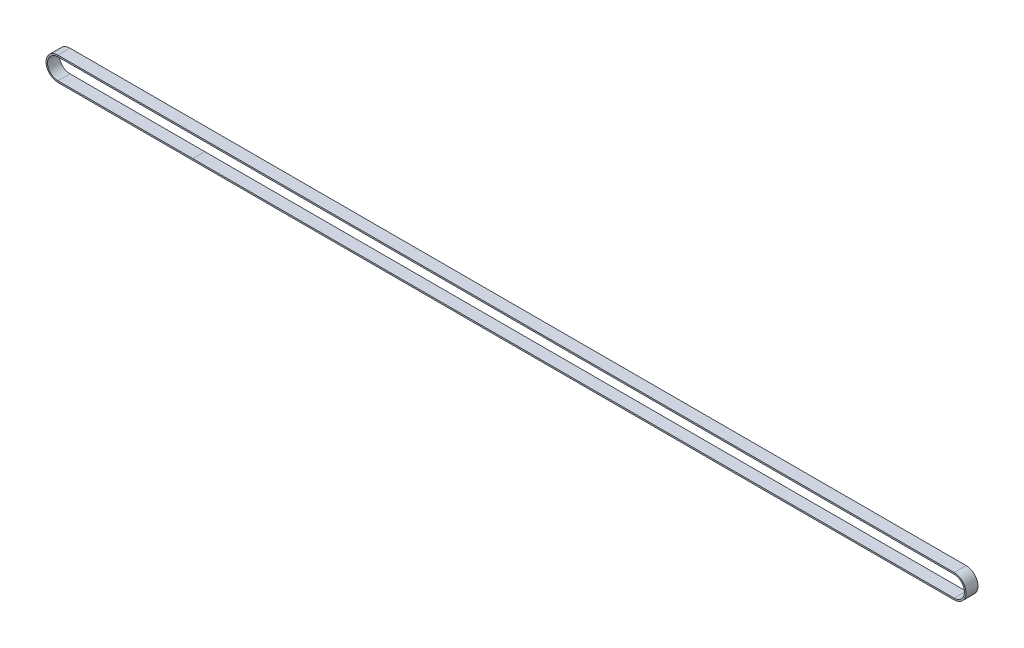
SolidWorks part; units mm, degrees
ref_plane "Front Plane" through (0, 0, 0) normal (0, 0, 1) x (1, 0, 0)
ref_plane "Top Plane" through (0, 0, 0) normal (0, 1, 0) x (1, 0, 0)
ref_plane "Right Plane" through (0, 0, 0) normal (1, 0, 0) x (0, 0, -1)
sketch "Sketch1" plane through (0, 0, 0) normal (0, 0, 1) x (1, 0, 0)
  line L0 (-149.0919, 9.0907) -> (296.9081, 9.0907)
  line L1 (-148.8622, -1.9593) -> (-148.9877, -1.9593)
  line L2 (-148.8622, -1.9593) -> (-148.8621, -1.9593)
  line L3 (-146.8622, -1.9593) -> (-146.8621, -1.9593)
  line L4 (-147.1989, -1.9593) -> (-146.8622, -1.9593)
  line L5 (-145.1989, -1.9593) -> (-144.8622, -1.9593)
  line L6 (-144.8622, -1.9593) -> (-144.8621, -1.9593)
  line L7 (-143.1989, -1.9593) -> (-142.8622, -1.9593)
  line L8 (-142.8622, -1.9593) -> (-142.8621, -1.9593)
  line L9 (-141.1989, -1.9593) -> (-140.8622, -1.9593)
  line L10 (-140.8622, -1.9593) -> (-140.8621, -1.9593)
  line L11 (-139.1989, -1.9593) -> (-138.8622, -1.9593)
  line L12 (-138.8622, -1.9593) -> (-138.8621, -1.9593)
  line L13 (-137.1989, -1.9593) -> (-136.8622, -1.9593)
  line L14 (-136.8622, -1.9593) -> (-136.8621, -1.9593)
  line L15 (-135.1989, -1.9593) -> (-134.8622, -1.9593)
  line L16 (-134.8622, -1.9593) -> (-134.8621, -1.9593)
  line L17 (-133.1989, -1.9593) -> (-132.8622, -1.9593)
  line L18 (-132.8622, -1.9593) -> (-132.8621, -1.9593)
  line L19 (-131.1989, -1.9593) -> (-130.8622, -1.9593)
  line L20 (-130.8622, -1.9593) -> (-130.8621, -1.9593)
  line L21 (-129.1989, -1.9593) -> (-128.8622, -1.9593)
  line L22 (-128.8622, -1.9593) -> (-128.8621, -1.9593)
  line L23 (-127.1989, -1.9593) -> (-126.8622, -1.9593)
  line L24 (-126.8622, -1.9593) -> (-126.8621, -1.9593)
  line L25 (-125.1989, -1.9593) -> (-124.8622, -1.9593)
  line L26 (-124.8622, -1.9593) -> (-124.8621, -1.9593)
  line L27 (-123.1989, -1.9593) -> (-122.8622, -1.9593)
  line L28 (-122.8622, -1.9593) -> (-122.8621, -1.9593)
  line L29 (-121.1989, -1.9593) -> (-120.8622, -1.9593)
  line L30 (-120.8622, -1.9593) -> (-120.8621, -1.9593)
  line L31 (-119.1989, -1.9593) -> (-118.8622, -1.9593)
  line L32 (-118.8622, -1.9593) -> (-118.8621, -1.9593)
  line L33 (-117.1989, -1.9593) -> (-116.8622, -1.9593)
  line L34 (-116.8622, -1.9593) -> (-116.8621, -1.9593)
  line L35 (-115.1989, -1.9593) -> (-114.8622, -1.9593)
  line L36 (-114.8622, -1.9593) -> (-114.8621, -1.9593)
  line L37 (-113.1989, -1.9593) -> (-112.8622, -1.9593)
  line L38 (-112.8622, -1.9593) -> (-112.8621, -1.9593)
  line L39 (-111.1989, -1.9593) -> (-110.8622, -1.9593)
  line L40 (-110.8622, -1.9593) -> (-110.8621, -1.9593)
  line L41 (-109.1989, -1.9593) -> (-108.8622, -1.9593)
  line L42 (-108.8622, -1.9593) -> (-108.8621, -1.9593)
  line L43 (-107.1989, -1.9593) -> (-106.8622, -1.9593)
  line L44 (-106.8622, -1.9593) -> (-106.8621, -1.9593)
  line L45 (-105.1989, -1.9593) -> (-104.8622, -1.9593)
  line L46 (-104.8622, -1.9593) -> (-104.8621, -1.9593)
  line L47 (-103.1989, -1.9593) -> (-102.8622, -1.9593)
  line L48 (-102.8622, -1.9593) -> (-102.8621, -1.9593)
  line L49 (-101.1989, -1.9593) -> (-100.8622, -1.9593)
  line L50 (-100.8622, -1.9593) -> (-100.8621, -1.9593)
  line L51 (-99.1989, -1.9593) -> (-98.8622, -1.9593)
  line L52 (-98.8622, -1.9593) -> (-98.8621, -1.9593)
  line L53 (-97.1989, -1.9593) -> (-96.8622, -1.9593)
  line L54 (-96.8622, -1.9593) -> (-96.8621, -1.9593)
  line L55 (-95.1989, -1.9593) -> (-94.8622, -1.9593)
  line L56 (-94.8622, -1.9593) -> (-94.8621, -1.9593)
  line L57 (-93.1989, -1.9593) -> (-92.8622, -1.9593)
  line L58 (-92.8622, -1.9593) -> (-92.8621, -1.9593)
  line L59 (-91.1989, -1.9593) -> (-90.8622, -1.9593)
  line L60 (-90.8622, -1.9593) -> (-90.8621, -1.9593)
  line L61 (-89.1989, -1.9593) -> (-88.8622, -1.9593)
  line L62 (-88.8622, -1.9593) -> (-88.8621, -1.9593)
  line L63 (-87.1989, -1.9593) -> (-86.8622, -1.9593)
  line L64 (-86.8622, -1.9593) -> (-86.8621, -1.9593)
  line L65 (-85.1989, -1.9593) -> (-84.8622, -1.9593)
  line L66 (-84.8622, -1.9593) -> (-84.8621, -1.9593)
  line L277 (296.9081, 3.1907) -> (-46.1296, 3.1907) construction
  line L278 (-83.1989, 8.3407) -> (296.9081, 8.3407)
  line L279 (-149.0919, -2.7093) -> (296.9081, -2.7093)
  line L280 (-149.1969, 8.3407) -> (-148.8622, 8.3407)
  line L491 (-84.8622, 8.3407) -> (-84.8621, 8.3407)
  line L492 (-85.1989, 8.3407) -> (-84.8622, 8.3407)
  line L493 (-86.8622, 8.3407) -> (-86.8621, 8.3407)
  line L494 (-87.1989, 8.3407) -> (-86.8622, 8.3407)
  line L495 (-88.8622, 8.3407) -> (-88.8621, 8.3407)
  line L496 (-89.1989, 8.3407) -> (-88.8622, 8.3407)
  line L497 (-90.8622, 8.3407) -> (-90.8621, 8.3407)
  line L498 (-91.1989, 8.3407) -> (-90.8622, 8.3407)
  line L499 (-92.8622, 8.3407) -> (-92.8621, 8.3407)
  line L500 (-93.1989, 8.3407) -> (-92.8622, 8.3407)
  line L501 (-94.8622, 8.3407) -> (-94.8621, 8.3407)
  line L502 (-95.1989, 8.3407) -> (-94.8622, 8.3407)
  line L503 (-96.8622, 8.3407) -> (-96.8621, 8.3407)
  line L504 (-97.1989, 8.3407) -> (-96.8622, 8.3407)
  line L505 (-98.8622, 8.3407) -> (-98.8621, 8.3407)
  line L506 (-99.1989, 8.3407) -> (-98.8622, 8.3407)
  line L507 (-100.8622, 8.3407) -> (-100.8621, 8.3407)
  line L508 (-101.1989, 8.3407) -> (-100.8622, 8.3407)
  line L509 (-102.8622, 8.3407) -> (-102.8621, 8.3407)
  line L510 (-103.1989, 8.3407) -> (-102.8622, 8.3407)
  line L511 (-104.8622, 8.3407) -> (-104.8621, 8.3407)
  line L512 (-105.1989, 8.3407) -> (-104.8622, 8.3407)
  line L513 (-106.8622, 8.3407) -> (-106.8621, 8.3407)
  line L514 (-107.1989, 8.3407) -> (-106.8622, 8.3407)
  line L515 (-108.8622, 8.3407) -> (-108.8621, 8.3407)
  line L516 (-109.1989, 8.3407) -> (-108.8622, 8.3407)
  line L517 (-110.8622, 8.3407) -> (-110.8621, 8.3407)
  line L518 (-111.1989, 8.3407) -> (-110.8622, 8.3407)
  line L519 (-112.8622, 8.3407) -> (-112.8621, 8.3407)
  line L520 (-113.1989, 8.3407) -> (-112.8622, 8.3407)
  line L521 (-114.8622, 8.3407) -> (-114.8621, 8.3407)
  line L522 (-115.1989, 8.3407) -> (-114.8622, 8.3407)
  line L523 (-116.8622, 8.3407) -> (-116.8621, 8.3407)
  line L524 (-117.1989, 8.3407) -> (-116.8622, 8.3407)
  line L525 (-118.8622, 8.3407) -> (-118.8621, 8.3407)
  line L526 (-119.1989, 8.3407) -> (-118.8622, 8.3407)
  line L527 (-120.8622, 8.3407) -> (-120.8621, 8.3407)
  line L528 (-121.1989, 8.3407) -> (-120.8622, 8.3407)
  line L529 (-122.8622, 8.3407) -> (-122.8621, 8.3407)
  line L530 (-123.1989, 8.3407) -> (-122.8622, 8.3407)
  line L531 (-124.8622, 8.3407) -> (-124.8621, 8.3407)
  line L532 (-125.1989, 8.3407) -> (-124.8622, 8.3407)
  line L533 (-126.8622, 8.3407) -> (-126.8621, 8.3407)
  line L534 (-127.1989, 8.3407) -> (-126.8622, 8.3407)
  line L535 (-128.8622, 8.3407) -> (-128.8621, 8.3407)
  line L536 (-129.1989, 8.3407) -> (-128.8622, 8.3407)
  line L537 (-130.8622, 8.3407) -> (-130.8621, 8.3407)
  line L538 (-131.1989, 8.3407) -> (-130.8622, 8.3407)
  line L539 (-132.8622, 8.3407) -> (-132.8621, 8.3407)
  line L540 (-133.1989, 8.3407) -> (-132.8622, 8.3407)
  line L541 (-134.8622, 8.3407) -> (-134.8621, 8.3407)
  line L542 (-135.1989, 8.3407) -> (-134.8622, 8.3407)
  line L543 (-136.8622, 8.3407) -> (-136.8621, 8.3407)
  line L544 (-137.1989, 8.3407) -> (-136.8622, 8.3407)
  line L545 (-138.8622, 8.3407) -> (-138.8621, 8.3407)
  line L546 (-139.1989, 8.3407) -> (-138.8622, 8.3407)
  line L547 (-140.8622, 8.3407) -> (-140.8621, 8.3407)
  line L548 (-141.1989, 8.3407) -> (-140.8622, 8.3407)
  line L549 (-142.8622, 8.3407) -> (-142.8621, 8.3407)
  line L550 (-143.1989, 8.3407) -> (-142.8622, 8.3407)
  line L551 (-144.8622, 8.3407) -> (-144.8621, 8.3407)
  line L552 (-145.1989, 8.3407) -> (-144.8622, 8.3407)
  line L553 (-147.1989, 8.3407) -> (-146.8622, 8.3407)
  line L554 (-146.8622, 8.3407) -> (-146.8621, 8.3407)
  line L555 (-148.8622, 8.3407) -> (-148.8621, 8.3407)
  line L556 (-83.1989, -1.9593) -> (296.9081, -1.9593)
  arc A0 (-149.1969, 8.3407) -> (-148.9869, -1.9593) centre (-149.0919, 3.1907) ccw
  arc A1 (296.9081, -1.9593) -> (296.9081, 8.3407) centre (296.9081, 3.1907) ccw
  arc A2 (-146.8621, -1.9593) -> (-146.7228, -1.8564) centre (-146.9197, -1.7354) ccw
  arc A3 (-148.8621, -1.9593) -> (-148.7228, -1.8564) centre (-148.9197, -1.7354) ccw
  arc A4 (-148.7228, -1.8564) -> (-148.6336, -1.611) centre (-149.2769, -1.5162) ccw
  arc A5 (-147.4274, -1.611) -> (-148.6336, -1.611) centre (-148.0305, -1.6999) ccw
  arc A6 (-147.4274, -1.611) -> (-147.3383, -1.8564) centre (-146.7842, -1.5162) ccw
  arc A7 (-147.3383, -1.8564) -> (-147.1989, -1.9593) centre (-147.1413, -1.7354) ccw
  arc A8 (-146.7228, -1.8564) -> (-146.6336, -1.611) centre (-147.2769, -1.5162) ccw
  arc A9 (-145.4274, -1.611) -> (-146.6336, -1.611) centre (-146.0305, -1.6999) ccw
  arc A10 (-145.4274, -1.611) -> (-145.3383, -1.8564) centre (-144.7842, -1.5162) ccw
  arc A11 (-145.3383, -1.8564) -> (-145.1989, -1.9593) centre (-145.1413, -1.7354) ccw
  arc A12 (-144.8621, -1.9593) -> (-144.7228, -1.8564) centre (-144.9197, -1.7354) ccw
  arc A13 (-144.7228, -1.8564) -> (-144.6336, -1.611) centre (-145.2769, -1.5162) ccw
  arc A14 (-143.4274, -1.611) -> (-144.6336, -1.611) centre (-144.0305, -1.6999) ccw
  arc A15 (-143.4274, -1.611) -> (-143.3383, -1.8564) centre (-142.7842, -1.5162) ccw
  arc A16 (-143.3383, -1.8564) -> (-143.1989, -1.9593) centre (-143.1413, -1.7354) ccw
  arc A17 (-142.8621, -1.9593) -> (-142.7228, -1.8564) centre (-142.9197, -1.7354) ccw
  arc A18 (-142.7228, -1.8564) -> (-142.6336, -1.611) centre (-143.2769, -1.5162) ccw
  arc A19 (-141.4274, -1.611) -> (-142.6336, -1.611) centre (-142.0305, -1.6999) ccw
  arc A20 (-141.4274, -1.611) -> (-141.3383, -1.8564) centre (-140.7842, -1.5162) ccw
  arc A21 (-141.3383, -1.8564) -> (-141.1989, -1.9593) centre (-141.1413, -1.7354) ccw
  arc A22 (-140.8621, -1.9593) -> (-140.7228, -1.8564) centre (-140.9197, -1.7354) ccw
  arc A23 (-140.7228, -1.8564) -> (-140.6336, -1.611) centre (-141.2769, -1.5162) ccw
  arc A24 (-139.4274, -1.611) -> (-140.6336, -1.611) centre (-140.0305, -1.6999) ccw
  arc A25 (-139.4274, -1.611) -> (-139.3383, -1.8564) centre (-138.7842, -1.5162) ccw
  arc A26 (-139.3383, -1.8564) -> (-139.1989, -1.9593) centre (-139.1413, -1.7354) ccw
  arc A27 (-138.8621, -1.9593) -> (-138.7228, -1.8564) centre (-138.9197, -1.7354) ccw
  arc A28 (-138.7228, -1.8564) -> (-138.6336, -1.611) centre (-139.2769, -1.5162) ccw
  arc A29 (-137.4274, -1.611) -> (-138.6336, -1.611) centre (-138.0305, -1.6999) ccw
  arc A30 (-137.4274, -1.611) -> (-137.3383, -1.8564) centre (-136.7842, -1.5162) ccw
  arc A31 (-137.3383, -1.8564) -> (-137.1989, -1.9593) centre (-137.1413, -1.7354) ccw
  arc A32 (-136.8621, -1.9593) -> (-136.7228, -1.8564) centre (-136.9197, -1.7354) ccw
  arc A33 (-136.7228, -1.8564) -> (-136.6336, -1.611) centre (-137.2769, -1.5162) ccw
  arc A34 (-135.4274, -1.611) -> (-136.6336, -1.611) centre (-136.0305, -1.6999) ccw
  arc A35 (-135.4274, -1.611) -> (-135.3383, -1.8564) centre (-134.7842, -1.5162) ccw
  arc A36 (-135.3383, -1.8564) -> (-135.1989, -1.9593) centre (-135.1413, -1.7354) ccw
  arc A37 (-134.8621, -1.9593) -> (-134.7228, -1.8564) centre (-134.9197, -1.7354) ccw
  arc A38 (-134.7228, -1.8564) -> (-134.6336, -1.611) centre (-135.2769, -1.5162) ccw
  arc A39 (-133.4274, -1.611) -> (-134.6336, -1.611) centre (-134.0305, -1.6999) ccw
  arc A40 (-133.4274, -1.611) -> (-133.3383, -1.8564) centre (-132.7842, -1.5162) ccw
  arc A41 (-133.3383, -1.8564) -> (-133.1989, -1.9593) centre (-133.1413, -1.7354) ccw
  arc A42 (-132.8621, -1.9593) -> (-132.7228, -1.8564) centre (-132.9197, -1.7354) ccw
  arc A43 (-132.7228, -1.8564) -> (-132.6336, -1.611) centre (-133.2769, -1.5162) ccw
  arc A44 (-131.4274, -1.611) -> (-132.6336, -1.611) centre (-132.0305, -1.6999) ccw
  arc A45 (-131.4274, -1.611) -> (-131.3383, -1.8564) centre (-130.7842, -1.5162) ccw
  arc A46 (-131.3383, -1.8564) -> (-131.1989, -1.9593) centre (-131.1413, -1.7354) ccw
  arc A47 (-130.8621, -1.9593) -> (-130.7228, -1.8564) centre (-130.9197, -1.7354) ccw
  arc A48 (-130.7228, -1.8564) -> (-130.6336, -1.611) centre (-131.2769, -1.5162) ccw
  arc A49 (-129.4274, -1.611) -> (-130.6336, -1.611) centre (-130.0305, -1.6999) ccw
  arc A50 (-129.4274, -1.611) -> (-129.3383, -1.8564) centre (-128.7842, -1.5162) ccw
  arc A51 (-129.3383, -1.8564) -> (-129.1989, -1.9593) centre (-129.1413, -1.7354) ccw
  arc A52 (-128.8621, -1.9593) -> (-128.7228, -1.8564) centre (-128.9197, -1.7354) ccw
  arc A53 (-128.7228, -1.8564) -> (-128.6336, -1.611) centre (-129.2769, -1.5162) ccw
  arc A54 (-127.4274, -1.611) -> (-128.6336, -1.611) centre (-128.0305, -1.6999) ccw
  arc A55 (-127.4274, -1.611) -> (-127.3383, -1.8564) centre (-126.7842, -1.5162) ccw
  arc A56 (-127.3383, -1.8564) -> (-127.1989, -1.9593) centre (-127.1413, -1.7354) ccw
  arc A57 (-126.8621, -1.9593) -> (-126.7228, -1.8564) centre (-126.9197, -1.7354) ccw
  arc A58 (-126.7228, -1.8564) -> (-126.6336, -1.611) centre (-127.2769, -1.5162) ccw
  arc A59 (-125.4274, -1.611) -> (-126.6336, -1.611) centre (-126.0305, -1.6999) ccw
  arc A60 (-125.4274, -1.611) -> (-125.3383, -1.8564) centre (-124.7842, -1.5162) ccw
  arc A61 (-125.3383, -1.8564) -> (-125.1989, -1.9593) centre (-125.1413, -1.7354) ccw
  arc A62 (-124.8621, -1.9593) -> (-124.7228, -1.8564) centre (-124.9197, -1.7354) ccw
  arc A63 (-124.7228, -1.8564) -> (-124.6336, -1.611) centre (-125.2769, -1.5162) ccw
  arc A64 (-123.4274, -1.611) -> (-124.6336, -1.611) centre (-124.0305, -1.6999) ccw
  arc A65 (-123.4274, -1.611) -> (-123.3383, -1.8564) centre (-122.7842, -1.5162) ccw
  arc A66 (-123.3383, -1.8564) -> (-123.1989, -1.9593) centre (-123.1413, -1.7354) ccw
  arc A67 (-122.8621, -1.9593) -> (-122.7228, -1.8564) centre (-122.9197, -1.7354) ccw
  arc A68 (-122.7228, -1.8564) -> (-122.6336, -1.611) centre (-123.2769, -1.5162) ccw
  arc A69 (-121.4274, -1.611) -> (-122.6336, -1.611) centre (-122.0305, -1.6999) ccw
  arc A70 (-121.4274, -1.611) -> (-121.3383, -1.8564) centre (-120.7842, -1.5162) ccw
  arc A71 (-121.3383, -1.8564) -> (-121.1989, -1.9593) centre (-121.1413, -1.7354) ccw
  arc A72 (-120.8621, -1.9593) -> (-120.7228, -1.8564) centre (-120.9197, -1.7354) ccw
  arc A73 (-120.7228, -1.8564) -> (-120.6336, -1.611) centre (-121.2769, -1.5162) ccw
  arc A74 (-119.4274, -1.611) -> (-120.6336, -1.611) centre (-120.0305, -1.6999) ccw
  arc A75 (-119.4274, -1.611) -> (-119.3383, -1.8564) centre (-118.7842, -1.5162) ccw
  arc A76 (-119.3383, -1.8564) -> (-119.1989, -1.9593) centre (-119.1413, -1.7354) ccw
  arc A77 (-118.8621, -1.9593) -> (-118.7228, -1.8564) centre (-118.9197, -1.7354) ccw
  arc A78 (-118.7228, -1.8564) -> (-118.6336, -1.611) centre (-119.2769, -1.5162) ccw
  arc A79 (-117.4274, -1.611) -> (-118.6336, -1.611) centre (-118.0305, -1.6999) ccw
  arc A80 (-117.4274, -1.611) -> (-117.3383, -1.8564) centre (-116.7842, -1.5162) ccw
  arc A81 (-117.3383, -1.8564) -> (-117.1989, -1.9593) centre (-117.1413, -1.7354) ccw
  arc A82 (-116.8621, -1.9593) -> (-116.7228, -1.8564) centre (-116.9197, -1.7354) ccw
  arc A83 (-116.7228, -1.8564) -> (-116.6336, -1.611) centre (-117.2769, -1.5162) ccw
  arc A84 (-115.4274, -1.611) -> (-116.6336, -1.611) centre (-116.0305, -1.6999) ccw
  arc A85 (-115.4274, -1.611) -> (-115.3383, -1.8564) centre (-114.7842, -1.5162) ccw
  arc A86 (-115.3383, -1.8564) -> (-115.1989, -1.9593) centre (-115.1413, -1.7354) ccw
  arc A87 (-114.8621, -1.9593) -> (-114.7228, -1.8564) centre (-114.9197, -1.7354) ccw
  arc A88 (-114.7228, -1.8564) -> (-114.6336, -1.611) centre (-115.2769, -1.5162) ccw
  arc A89 (-113.4274, -1.611) -> (-114.6336, -1.611) centre (-114.0305, -1.6999) ccw
  arc A90 (-113.4274, -1.611) -> (-113.3383, -1.8564) centre (-112.7842, -1.5162) ccw
  arc A91 (-113.3383, -1.8564) -> (-113.1989, -1.9593) centre (-113.1413, -1.7354) ccw
  arc A92 (-112.8621, -1.9593) -> (-112.7228, -1.8564) centre (-112.9197, -1.7354) ccw
  arc A93 (-112.7228, -1.8564) -> (-112.6336, -1.611) centre (-113.2769, -1.5162) ccw
  arc A94 (-111.4274, -1.611) -> (-112.6336, -1.611) centre (-112.0305, -1.6999) ccw
  arc A95 (-111.4274, -1.611) -> (-111.3383, -1.8564) centre (-110.7842, -1.5162) ccw
  arc A96 (-111.3383, -1.8564) -> (-111.1989, -1.9593) centre (-111.1413, -1.7354) ccw
  arc A97 (-110.8621, -1.9593) -> (-110.7228, -1.8564) centre (-110.9197, -1.7354) ccw
  arc A98 (-110.7228, -1.8564) -> (-110.6336, -1.611) centre (-111.2769, -1.5162) ccw
  arc A99 (-109.4274, -1.611) -> (-110.6336, -1.611) centre (-110.0305, -1.6999) ccw
  arc A100 (-109.4274, -1.611) -> (-109.3383, -1.8564) centre (-108.7842, -1.5162) ccw
  arc A101 (-109.3383, -1.8564) -> (-109.1989, -1.9593) centre (-109.1413, -1.7354) ccw
  arc A102 (-108.8621, -1.9593) -> (-108.7228, -1.8564) centre (-108.9197, -1.7354) ccw
  arc A103 (-108.7228, -1.8564) -> (-108.6336, -1.611) centre (-109.2769, -1.5162) ccw
  arc A104 (-107.4274, -1.611) -> (-108.6336, -1.611) centre (-108.0305, -1.6999) ccw
  arc A105 (-107.4274, -1.611) -> (-107.3383, -1.8564) centre (-106.7842, -1.5162) ccw
  arc A106 (-107.3383, -1.8564) -> (-107.1989, -1.9593) centre (-107.1413, -1.7354) ccw
  arc A107 (-106.8621, -1.9593) -> (-106.7228, -1.8564) centre (-106.9197, -1.7354) ccw
  arc A108 (-106.7228, -1.8564) -> (-106.6336, -1.611) centre (-107.2769, -1.5162) ccw
  arc A109 (-105.4274, -1.611) -> (-106.6336, -1.611) centre (-106.0305, -1.6999) ccw
  arc A110 (-105.4274, -1.611) -> (-105.3383, -1.8564) centre (-104.7842, -1.5162) ccw
  arc A111 (-105.3383, -1.8564) -> (-105.1989, -1.9593) centre (-105.1413, -1.7354) ccw
  arc A112 (-104.8621, -1.9593) -> (-104.7228, -1.8564) centre (-104.9197, -1.7354) ccw
  arc A113 (-104.7228, -1.8564) -> (-104.6336, -1.611) centre (-105.2769, -1.5162) ccw
  arc A114 (-103.4274, -1.611) -> (-104.6336, -1.611) centre (-104.0305, -1.6999) ccw
  arc A115 (-103.4274, -1.611) -> (-103.3383, -1.8564) centre (-102.7842, -1.5162) ccw
  arc A116 (-103.3383, -1.8564) -> (-103.1989, -1.9593) centre (-103.1413, -1.7354) ccw
  arc A117 (-102.8621, -1.9593) -> (-102.7228, -1.8564) centre (-102.9197, -1.7354) ccw
  arc A118 (-102.7228, -1.8564) -> (-102.6336, -1.611) centre (-103.2769, -1.5162) ccw
  arc A119 (-101.4274, -1.611) -> (-102.6336, -1.611) centre (-102.0305, -1.6999) ccw
  arc A120 (-101.4274, -1.611) -> (-101.3383, -1.8564) centre (-100.7842, -1.5162) ccw
  arc A121 (-101.3383, -1.8564) -> (-101.1989, -1.9593) centre (-101.1413, -1.7354) ccw
  arc A122 (-100.8621, -1.9593) -> (-100.7228, -1.8564) centre (-100.9197, -1.7354) ccw
  arc A123 (-100.7228, -1.8564) -> (-100.6336, -1.611) centre (-101.2769, -1.5162) ccw
  arc A124 (-99.4274, -1.611) -> (-100.6336, -1.611) centre (-100.0305, -1.6999) ccw
  arc A125 (-99.4274, -1.611) -> (-99.3383, -1.8564) centre (-98.7842, -1.5162) ccw
  arc A126 (-99.3383, -1.8564) -> (-99.1989, -1.9593) centre (-99.1413, -1.7354) ccw
  arc A127 (-98.8621, -1.9593) -> (-98.7228, -1.8564) centre (-98.9197, -1.7354) ccw
  arc A128 (-98.7228, -1.8564) -> (-98.6336, -1.611) centre (-99.2769, -1.5162) ccw
  arc A129 (-97.4274, -1.611) -> (-98.6336, -1.611) centre (-98.0305, -1.6999) ccw
  arc A130 (-97.4274, -1.611) -> (-97.3383, -1.8564) centre (-96.7842, -1.5162) ccw
  arc A131 (-97.3383, -1.8564) -> (-97.1989, -1.9593) centre (-97.1413, -1.7354) ccw
  arc A132 (-96.8621, -1.9593) -> (-96.7228, -1.8564) centre (-96.9197, -1.7354) ccw
  arc A133 (-96.7228, -1.8564) -> (-96.6336, -1.611) centre (-97.2769, -1.5162) ccw
  arc A134 (-95.4274, -1.611) -> (-96.6336, -1.611) centre (-96.0305, -1.6999) ccw
  arc A135 (-95.4274, -1.611) -> (-95.3383, -1.8564) centre (-94.7842, -1.5162) ccw
  arc A136 (-95.3383, -1.8564) -> (-95.1989, -1.9593) centre (-95.1413, -1.7354) ccw
  arc A137 (-94.8621, -1.9593) -> (-94.7228, -1.8564) centre (-94.9197, -1.7354) ccw
  arc A138 (-94.7228, -1.8564) -> (-94.6336, -1.611) centre (-95.2769, -1.5162) ccw
  arc A139 (-93.4274, -1.611) -> (-94.6336, -1.611) centre (-94.0305, -1.6999) ccw
  arc A140 (-93.4274, -1.611) -> (-93.3383, -1.8564) centre (-92.7842, -1.5162) ccw
  arc A141 (-93.3383, -1.8564) -> (-93.1989, -1.9593) centre (-93.1413, -1.7354) ccw
  arc A142 (-92.8621, -1.9593) -> (-92.7228, -1.8564) centre (-92.9197, -1.7354) ccw
  arc A143 (-92.7228, -1.8564) -> (-92.6336, -1.611) centre (-93.2769, -1.5162) ccw
  arc A144 (-91.4274, -1.611) -> (-92.6336, -1.611) centre (-92.0305, -1.6999) ccw
  arc A145 (-91.4274, -1.611) -> (-91.3383, -1.8564) centre (-90.7842, -1.5162) ccw
  arc A146 (-91.3383, -1.8564) -> (-91.1989, -1.9593) centre (-91.1413, -1.7354) ccw
  arc A147 (-90.8621, -1.9593) -> (-90.7228, -1.8564) centre (-90.9197, -1.7354) ccw
  arc A148 (-90.7228, -1.8564) -> (-90.6336, -1.611) centre (-91.2769, -1.5162) ccw
  arc A149 (-89.4274, -1.611) -> (-90.6336, -1.611) centre (-90.0305, -1.6999) ccw
  arc A150 (-89.4274, -1.611) -> (-89.3383, -1.8564) centre (-88.7842, -1.5162) ccw
  arc A151 (-89.3383, -1.8564) -> (-89.1989, -1.9593) centre (-89.1413, -1.7354) ccw
  arc A152 (-88.8621, -1.9593) -> (-88.7228, -1.8564) centre (-88.9197, -1.7354) ccw
  arc A153 (-88.7228, -1.8564) -> (-88.6336, -1.611) centre (-89.2769, -1.5162) ccw
  arc A154 (-87.4274, -1.611) -> (-88.6336, -1.611) centre (-88.0305, -1.6999) ccw
  arc A155 (-87.4274, -1.611) -> (-87.3383, -1.8564) centre (-86.7842, -1.5162) ccw
  arc A156 (-87.3383, -1.8564) -> (-87.1989, -1.9593) centre (-87.1413, -1.7354) ccw
  arc A157 (-86.8621, -1.9593) -> (-86.7228, -1.8564) centre (-86.9197, -1.7354) ccw
  arc A158 (-86.7228, -1.8564) -> (-86.6336, -1.611) centre (-87.2769, -1.5162) ccw
  arc A159 (-85.4274, -1.611) -> (-86.6336, -1.611) centre (-86.0305, -1.6999) ccw
  arc A160 (-85.4274, -1.611) -> (-85.3383, -1.8564) centre (-84.7842, -1.5162) ccw
  arc A161 (-85.3383, -1.8564) -> (-85.1989, -1.9593) centre (-85.1413, -1.7354) ccw
  arc A162 (-84.8621, -1.9593) -> (-84.7228, -1.8564) centre (-84.9197, -1.7354) ccw
  arc A163 (-84.7228, -1.8564) -> (-84.6336, -1.611) centre (-85.2769, -1.5162) ccw
  arc A164 (-83.4274, -1.611) -> (-84.6336, -1.611) centre (-84.0305, -1.6999) ccw
  arc A165 (-83.4274, -1.611) -> (-83.3383, -1.8564) centre (-82.7842, -1.5162) ccw
  arc A166 (-83.3383, -1.8564) -> (-83.1989, -1.9593) centre (-83.1413, -1.7354) ccw
  arc A692 (-149.0919, 9.0907) -> (-149.0919, -2.7093) centre (-149.0919, 3.1907) ccw
  arc A693 (296.9081, -2.7093) -> (296.9081, 9.0907) centre (296.9081, 3.1907) ccw
  arc A1219 (-83.3383, 8.2378) -> (-83.1989, 8.3407) centre (-83.1413, 8.1169) cw
  arc A1220 (-83.4274, 7.9924) -> (-83.3383, 8.2378) centre (-82.7842, 7.8976) cw
  arc A1221 (-83.4274, 7.9924) -> (-84.6336, 7.9924) centre (-84.0305, 8.0813) cw
  arc A1222 (-84.7228, 8.2378) -> (-84.6336, 7.9924) centre (-85.2769, 7.8976) cw
  arc A1223 (-84.8621, 8.3407) -> (-84.7228, 8.2378) centre (-84.9197, 8.1169) cw
  arc A1224 (-85.3383, 8.2378) -> (-85.1989, 8.3407) centre (-85.1413, 8.1169) cw
  arc A1225 (-85.4274, 7.9924) -> (-85.3383, 8.2378) centre (-84.7842, 7.8976) cw
  arc A1226 (-85.4274, 7.9924) -> (-86.6336, 7.9924) centre (-86.0305, 8.0813) cw
  arc A1227 (-86.7228, 8.2378) -> (-86.6336, 7.9924) centre (-87.2769, 7.8976) cw
  arc A1228 (-86.8621, 8.3407) -> (-86.7228, 8.2378) centre (-86.9197, 8.1169) cw
  arc A1229 (-87.3383, 8.2378) -> (-87.1989, 8.3407) centre (-87.1413, 8.1169) cw
  arc A1230 (-87.4274, 7.9924) -> (-87.3383, 8.2378) centre (-86.7842, 7.8976) cw
  arc A1231 (-87.4274, 7.9924) -> (-88.6336, 7.9924) centre (-88.0305, 8.0813) cw
  arc A1232 (-88.7228, 8.2378) -> (-88.6336, 7.9924) centre (-89.2769, 7.8976) cw
  arc A1233 (-88.8621, 8.3407) -> (-88.7228, 8.2378) centre (-88.9197, 8.1169) cw
  arc A1234 (-89.3383, 8.2378) -> (-89.1989, 8.3407) centre (-89.1413, 8.1169) cw
  arc A1235 (-89.4274, 7.9924) -> (-89.3383, 8.2378) centre (-88.7842, 7.8976) cw
  arc A1236 (-89.4274, 7.9924) -> (-90.6336, 7.9924) centre (-90.0305, 8.0813) cw
  arc A1237 (-90.7228, 8.2378) -> (-90.6336, 7.9924) centre (-91.2769, 7.8976) cw
  arc A1238 (-90.8621, 8.3407) -> (-90.7228, 8.2378) centre (-90.9197, 8.1169) cw
  arc A1239 (-91.3383, 8.2378) -> (-91.1989, 8.3407) centre (-91.1413, 8.1169) cw
  arc A1240 (-91.4274, 7.9924) -> (-91.3383, 8.2378) centre (-90.7842, 7.8976) cw
  arc A1241 (-91.4274, 7.9924) -> (-92.6336, 7.9924) centre (-92.0305, 8.0813) cw
  arc A1242 (-92.7228, 8.2378) -> (-92.6336, 7.9924) centre (-93.2769, 7.8976) cw
  arc A1243 (-92.8621, 8.3407) -> (-92.7228, 8.2378) centre (-92.9197, 8.1169) cw
  arc A1244 (-93.3383, 8.2378) -> (-93.1989, 8.3407) centre (-93.1413, 8.1169) cw
  arc A1245 (-93.4274, 7.9924) -> (-93.3383, 8.2378) centre (-92.7842, 7.8976) cw
  arc A1246 (-93.4274, 7.9924) -> (-94.6336, 7.9924) centre (-94.0305, 8.0813) cw
  arc A1247 (-94.7228, 8.2378) -> (-94.6336, 7.9924) centre (-95.2769, 7.8976) cw
  arc A1248 (-94.8621, 8.3407) -> (-94.7228, 8.2378) centre (-94.9197, 8.1169) cw
  arc A1249 (-95.3383, 8.2378) -> (-95.1989, 8.3407) centre (-95.1413, 8.1169) cw
  arc A1250 (-95.4274, 7.9924) -> (-95.3383, 8.2378) centre (-94.7842, 7.8976) cw
  arc A1251 (-95.4274, 7.9924) -> (-96.6336, 7.9924) centre (-96.0305, 8.0813) cw
  arc A1252 (-96.7228, 8.2378) -> (-96.6336, 7.9924) centre (-97.2769, 7.8976) cw
  arc A1253 (-96.8621, 8.3407) -> (-96.7228, 8.2378) centre (-96.9197, 8.1169) cw
  arc A1254 (-97.3383, 8.2378) -> (-97.1989, 8.3407) centre (-97.1413, 8.1169) cw
  arc A1255 (-97.4274, 7.9924) -> (-97.3383, 8.2378) centre (-96.7842, 7.8976) cw
  arc A1256 (-97.4274, 7.9924) -> (-98.6336, 7.9924) centre (-98.0305, 8.0813) cw
  arc A1257 (-98.7228, 8.2378) -> (-98.6336, 7.9924) centre (-99.2769, 7.8976) cw
  arc A1258 (-98.8621, 8.3407) -> (-98.7228, 8.2378) centre (-98.9197, 8.1169) cw
  arc A1259 (-99.3383, 8.2378) -> (-99.1989, 8.3407) centre (-99.1413, 8.1169) cw
  arc A1260 (-99.4274, 7.9924) -> (-99.3383, 8.2378) centre (-98.7842, 7.8976) cw
  arc A1261 (-99.4274, 7.9924) -> (-100.6336, 7.9924) centre (-100.0305, 8.0813) cw
  arc A1262 (-100.7228, 8.2378) -> (-100.6336, 7.9924) centre (-101.2769, 7.8976) cw
  arc A1263 (-100.8621, 8.3407) -> (-100.7228, 8.2378) centre (-100.9197, 8.1169) cw
  arc A1264 (-101.3383, 8.2378) -> (-101.1989, 8.3407) centre (-101.1413, 8.1169) cw
  arc A1265 (-101.4274, 7.9924) -> (-101.3383, 8.2378) centre (-100.7842, 7.8976) cw
  arc A1266 (-101.4274, 7.9924) -> (-102.6336, 7.9924) centre (-102.0305, 8.0813) cw
  arc A1267 (-102.7228, 8.2378) -> (-102.6336, 7.9924) centre (-103.2769, 7.8976) cw
  arc A1268 (-102.8621, 8.3407) -> (-102.7228, 8.2378) centre (-102.9197, 8.1169) cw
  arc A1269 (-103.3383, 8.2378) -> (-103.1989, 8.3407) centre (-103.1413, 8.1169) cw
  arc A1270 (-103.4274, 7.9924) -> (-103.3383, 8.2378) centre (-102.7842, 7.8976) cw
  arc A1271 (-103.4274, 7.9924) -> (-104.6336, 7.9924) centre (-104.0305, 8.0813) cw
  arc A1272 (-104.7228, 8.2378) -> (-104.6336, 7.9924) centre (-105.2769, 7.8976) cw
  arc A1273 (-104.8621, 8.3407) -> (-104.7228, 8.2378) centre (-104.9197, 8.1169) cw
  arc A1274 (-105.3383, 8.2378) -> (-105.1989, 8.3407) centre (-105.1413, 8.1169) cw
  arc A1275 (-105.4274, 7.9924) -> (-105.3383, 8.2378) centre (-104.7842, 7.8976) cw
  arc A1276 (-105.4274, 7.9924) -> (-106.6336, 7.9924) centre (-106.0305, 8.0813) cw
  arc A1277 (-106.7228, 8.2378) -> (-106.6336, 7.9924) centre (-107.2769, 7.8976) cw
  arc A1278 (-106.8621, 8.3407) -> (-106.7228, 8.2378) centre (-106.9197, 8.1169) cw
  arc A1279 (-107.3383, 8.2378) -> (-107.1989, 8.3407) centre (-107.1413, 8.1169) cw
  arc A1280 (-107.4274, 7.9924) -> (-107.3383, 8.2378) centre (-106.7842, 7.8976) cw
  arc A1281 (-107.4274, 7.9924) -> (-108.6336, 7.9924) centre (-108.0305, 8.0813) cw
  arc A1282 (-108.7228, 8.2378) -> (-108.6336, 7.9924) centre (-109.2769, 7.8976) cw
  arc A1283 (-108.8621, 8.3407) -> (-108.7228, 8.2378) centre (-108.9197, 8.1169) cw
  arc A1284 (-109.3383, 8.2378) -> (-109.1989, 8.3407) centre (-109.1413, 8.1169) cw
  arc A1285 (-109.4274, 7.9924) -> (-109.3383, 8.2378) centre (-108.7842, 7.8976) cw
  arc A1286 (-109.4274, 7.9924) -> (-110.6336, 7.9924) centre (-110.0305, 8.0813) cw
  arc A1287 (-110.7228, 8.2378) -> (-110.6336, 7.9924) centre (-111.2769, 7.8976) cw
  arc A1288 (-110.8621, 8.3407) -> (-110.7228, 8.2378) centre (-110.9197, 8.1169) cw
  arc A1289 (-111.3383, 8.2378) -> (-111.1989, 8.3407) centre (-111.1413, 8.1169) cw
  arc A1290 (-111.4274, 7.9924) -> (-111.3383, 8.2378) centre (-110.7842, 7.8976) cw
  arc A1291 (-111.4274, 7.9924) -> (-112.6336, 7.9924) centre (-112.0305, 8.0813) cw
  arc A1292 (-112.7228, 8.2378) -> (-112.6336, 7.9924) centre (-113.2769, 7.8976) cw
  arc A1293 (-112.8621, 8.3407) -> (-112.7228, 8.2378) centre (-112.9197, 8.1169) cw
  arc A1294 (-113.3383, 8.2378) -> (-113.1989, 8.3407) centre (-113.1413, 8.1169) cw
  arc A1295 (-113.4274, 7.9924) -> (-113.3383, 8.2378) centre (-112.7842, 7.8976) cw
  arc A1296 (-113.4274, 7.9924) -> (-114.6336, 7.9924) centre (-114.0305, 8.0813) cw
  arc A1297 (-114.7228, 8.2378) -> (-114.6336, 7.9924) centre (-115.2769, 7.8976) cw
  arc A1298 (-114.8621, 8.3407) -> (-114.7228, 8.2378) centre (-114.9197, 8.1169) cw
  arc A1299 (-115.3383, 8.2378) -> (-115.1989, 8.3407) centre (-115.1413, 8.1169) cw
  arc A1300 (-115.4274, 7.9924) -> (-115.3383, 8.2378) centre (-114.7842, 7.8976) cw
  arc A1301 (-115.4274, 7.9924) -> (-116.6336, 7.9924) centre (-116.0305, 8.0813) cw
  arc A1302 (-116.7228, 8.2378) -> (-116.6336, 7.9924) centre (-117.2769, 7.8976) cw
  arc A1303 (-116.8621, 8.3407) -> (-116.7228, 8.2378) centre (-116.9197, 8.1169) cw
  arc A1304 (-117.3383, 8.2378) -> (-117.1989, 8.3407) centre (-117.1413, 8.1169) cw
  arc A1305 (-117.4274, 7.9924) -> (-117.3383, 8.2378) centre (-116.7842, 7.8976) cw
  arc A1306 (-117.4274, 7.9924) -> (-118.6336, 7.9924) centre (-118.0305, 8.0813) cw
  arc A1307 (-118.7228, 8.2378) -> (-118.6336, 7.9924) centre (-119.2769, 7.8976) cw
  arc A1308 (-118.8621, 8.3407) -> (-118.7228, 8.2378) centre (-118.9197, 8.1169) cw
  arc A1309 (-119.3383, 8.2378) -> (-119.1989, 8.3407) centre (-119.1413, 8.1169) cw
  arc A1310 (-119.4274, 7.9924) -> (-119.3383, 8.2378) centre (-118.7842, 7.8976) cw
  arc A1311 (-119.4274, 7.9924) -> (-120.6336, 7.9924) centre (-120.0305, 8.0813) cw
  arc A1312 (-120.7228, 8.2378) -> (-120.6336, 7.9924) centre (-121.2769, 7.8976) cw
  arc A1313 (-120.8621, 8.3407) -> (-120.7228, 8.2378) centre (-120.9197, 8.1169) cw
  arc A1314 (-121.3383, 8.2378) -> (-121.1989, 8.3407) centre (-121.1413, 8.1169) cw
  arc A1315 (-121.4274, 7.9924) -> (-121.3383, 8.2378) centre (-120.7842, 7.8976) cw
  arc A1316 (-121.4274, 7.9924) -> (-122.6336, 7.9924) centre (-122.0305, 8.0813) cw
  arc A1317 (-122.7228, 8.2378) -> (-122.6336, 7.9924) centre (-123.2769, 7.8976) cw
  arc A1318 (-122.8621, 8.3407) -> (-122.7228, 8.2378) centre (-122.9197, 8.1169) cw
  arc A1319 (-123.3383, 8.2378) -> (-123.1989, 8.3407) centre (-123.1413, 8.1169) cw
  arc A1320 (-123.4274, 7.9924) -> (-123.3383, 8.2378) centre (-122.7842, 7.8976) cw
  arc A1321 (-123.4274, 7.9924) -> (-124.6336, 7.9924) centre (-124.0305, 8.0813) cw
  arc A1322 (-124.7228, 8.2378) -> (-124.6336, 7.9924) centre (-125.2769, 7.8976) cw
  arc A1323 (-124.8621, 8.3407) -> (-124.7228, 8.2378) centre (-124.9197, 8.1169) cw
  arc A1324 (-125.3383, 8.2378) -> (-125.1989, 8.3407) centre (-125.1413, 8.1169) cw
  arc A1325 (-125.4274, 7.9924) -> (-125.3383, 8.2378) centre (-124.7842, 7.8976) cw
  arc A1326 (-125.4274, 7.9924) -> (-126.6336, 7.9924) centre (-126.0305, 8.0813) cw
  arc A1327 (-126.7228, 8.2378) -> (-126.6336, 7.9924) centre (-127.2769, 7.8976) cw
  arc A1328 (-126.8621, 8.3407) -> (-126.7228, 8.2378) centre (-126.9197, 8.1169) cw
  arc A1329 (-127.3383, 8.2378) -> (-127.1989, 8.3407) centre (-127.1413, 8.1169) cw
  arc A1330 (-127.4274, 7.9924) -> (-127.3383, 8.2378) centre (-126.7842, 7.8976) cw
  arc A1331 (-127.4274, 7.9924) -> (-128.6336, 7.9924) centre (-128.0305, 8.0813) cw
  arc A1332 (-128.7228, 8.2378) -> (-128.6336, 7.9924) centre (-129.2769, 7.8976) cw
  arc A1333 (-128.8621, 8.3407) -> (-128.7228, 8.2378) centre (-128.9197, 8.1169) cw
  arc A1334 (-129.3383, 8.2378) -> (-129.1989, 8.3407) centre (-129.1413, 8.1169) cw
  arc A1335 (-129.4274, 7.9924) -> (-129.3383, 8.2378) centre (-128.7842, 7.8976) cw
  arc A1336 (-129.4274, 7.9924) -> (-130.6336, 7.9924) centre (-130.0305, 8.0813) cw
  arc A1337 (-130.7228, 8.2378) -> (-130.6336, 7.9924) centre (-131.2769, 7.8976) cw
  arc A1338 (-130.8621, 8.3407) -> (-130.7228, 8.2378) centre (-130.9197, 8.1169) cw
  arc A1339 (-131.3383, 8.2378) -> (-131.1989, 8.3407) centre (-131.1413, 8.1169) cw
  arc A1340 (-131.4274, 7.9924) -> (-131.3383, 8.2378) centre (-130.7842, 7.8976) cw
  arc A1341 (-131.4274, 7.9924) -> (-132.6336, 7.9924) centre (-132.0305, 8.0813) cw
  arc A1342 (-132.7228, 8.2378) -> (-132.6336, 7.9924) centre (-133.2769, 7.8976) cw
  arc A1343 (-132.8621, 8.3407) -> (-132.7228, 8.2378) centre (-132.9197, 8.1169) cw
  arc A1344 (-133.3383, 8.2378) -> (-133.1989, 8.3407) centre (-133.1413, 8.1169) cw
  arc A1345 (-133.4274, 7.9924) -> (-133.3383, 8.2378) centre (-132.7842, 7.8976) cw
  arc A1346 (-133.4274, 7.9924) -> (-134.6336, 7.9924) centre (-134.0305, 8.0813) cw
  arc A1347 (-134.7228, 8.2378) -> (-134.6336, 7.9924) centre (-135.2769, 7.8976) cw
  arc A1348 (-134.8621, 8.3407) -> (-134.7228, 8.2378) centre (-134.9197, 8.1169) cw
  arc A1349 (-135.3383, 8.2378) -> (-135.1989, 8.3407) centre (-135.1413, 8.1169) cw
  arc A1350 (-135.4274, 7.9924) -> (-135.3383, 8.2378) centre (-134.7842, 7.8976) cw
  arc A1351 (-135.4274, 7.9924) -> (-136.6336, 7.9924) centre (-136.0305, 8.0813) cw
  arc A1352 (-136.7228, 8.2378) -> (-136.6336, 7.9924) centre (-137.2769, 7.8976) cw
  arc A1353 (-136.8621, 8.3407) -> (-136.7228, 8.2378) centre (-136.9197, 8.1169) cw
  arc A1354 (-137.3383, 8.2378) -> (-137.1989, 8.3407) centre (-137.1413, 8.1169) cw
  arc A1355 (-137.4274, 7.9924) -> (-137.3383, 8.2378) centre (-136.7842, 7.8976) cw
  arc A1356 (-137.4274, 7.9924) -> (-138.6336, 7.9924) centre (-138.0305, 8.0813) cw
  arc A1357 (-138.7228, 8.2378) -> (-138.6336, 7.9924) centre (-139.2769, 7.8976) cw
  arc A1358 (-138.8621, 8.3407) -> (-138.7228, 8.2378) centre (-138.9197, 8.1169) cw
  arc A1359 (-139.3383, 8.2378) -> (-139.1989, 8.3407) centre (-139.1413, 8.1169) cw
  arc A1360 (-139.4274, 7.9924) -> (-139.3383, 8.2378) centre (-138.7842, 7.8976) cw
  arc A1361 (-139.4274, 7.9924) -> (-140.6336, 7.9924) centre (-140.0305, 8.0813) cw
  arc A1362 (-140.7228, 8.2378) -> (-140.6336, 7.9924) centre (-141.2769, 7.8976) cw
  arc A1363 (-140.8621, 8.3407) -> (-140.7228, 8.2378) centre (-140.9197, 8.1169) cw
  arc A1364 (-141.3383, 8.2378) -> (-141.1989, 8.3407) centre (-141.1413, 8.1169) cw
  arc A1365 (-141.4274, 7.9924) -> (-141.3383, 8.2378) centre (-140.7842, 7.8976) cw
  arc A1366 (-141.4274, 7.9924) -> (-142.6336, 7.9924) centre (-142.0305, 8.0813) cw
  arc A1367 (-142.7228, 8.2378) -> (-142.6336, 7.9924) centre (-143.2769, 7.8976) cw
  arc A1368 (-142.8621, 8.3407) -> (-142.7228, 8.2378) centre (-142.9197, 8.1169) cw
  arc A1369 (-143.3383, 8.2378) -> (-143.1989, 8.3407) centre (-143.1413, 8.1169) cw
  arc A1370 (-143.4274, 7.9924) -> (-143.3383, 8.2378) centre (-142.7842, 7.8976) cw
  arc A1371 (-143.4274, 7.9924) -> (-144.6336, 7.9924) centre (-144.0305, 8.0813) cw
  arc A1372 (-144.7228, 8.2378) -> (-144.6336, 7.9924) centre (-145.2769, 7.8976) cw
  arc A1373 (-144.8621, 8.3407) -> (-144.7228, 8.2378) centre (-144.9197, 8.1169) cw
  arc A1374 (-145.3383, 8.2378) -> (-145.1989, 8.3407) centre (-145.1413, 8.1169) cw
  arc A1375 (-145.4274, 7.9924) -> (-145.3383, 8.2378) centre (-144.7842, 7.8976) cw
  arc A1376 (-145.4274, 7.9924) -> (-146.6336, 7.9924) centre (-146.0305, 8.0813) cw
  arc A1377 (-146.7228, 8.2378) -> (-146.6336, 7.9924) centre (-147.2769, 7.8976) cw
  arc A1378 (-147.3383, 8.2378) -> (-147.1989, 8.3407) centre (-147.1413, 8.1169) cw
  arc A1379 (-147.4274, 7.9924) -> (-147.3383, 8.2378) centre (-146.7842, 7.8976) cw
  arc A1380 (-147.4274, 7.9924) -> (-148.6336, 7.9924) centre (-148.0305, 8.0813) cw
  arc A1381 (-148.7228, 8.2378) -> (-148.6336, 7.9924) centre (-149.2769, 7.8976) cw
  arc A1382 (-148.8621, 8.3407) -> (-148.7228, 8.2378) centre (-148.9197, 8.1169) cw
  arc A1383 (-146.8621, 8.3407) -> (-146.7228, 8.2378) centre (-146.9197, 8.1169) cw
  dimension "D1" = 446
extrude "Boss-Extrude1" add sketch "Sketch1" along normal blind 6 contours L554 A1383 A1377 A1376 A1375 A1374 L552 L551 A1373 A1372 A1371 A1370 A1369 L550 L549 A1368 A1367 A1366 A1365 A1364 L548 L547 A1363 A1362 A1361 A1360 A1359 L546 L545 A1358 A1357 A1356 A1355 A1354 L544 L543 A1353 A1352 A1351 A1350 A1349 L542 L541 A1348 A1347
sketch "草图1" plane through (0, 0, 6) normal (0, 0, 1) x (1, 0, 0)
  line L0 (-81.9664, 8.3407) -> (-149.1969, 8.3407)
  line L1 (-83.1989, 8.3407) -> (296.9081, 8.3407) construction
  line L2 (-149.1969, 8.3407) -> (-149.0919, -1.9604)
  line L3 (-149.0919, -1.9604) -> (-81.9664, -1.9593)
  line L5 (-81.9664, -1.9593) -> (-81.9664, 8.3407)
  line L6 (-83.1989, -1.9593) -> (296.9081, -1.9593) construction
  arc A0 (-149.1969, 8.3407) -> (-148.9877, -1.9593) centre (-149.0919, 3.1907) ccw construction
extrude "切除-拉伸2" cut sketch "草图1" against normal through all
